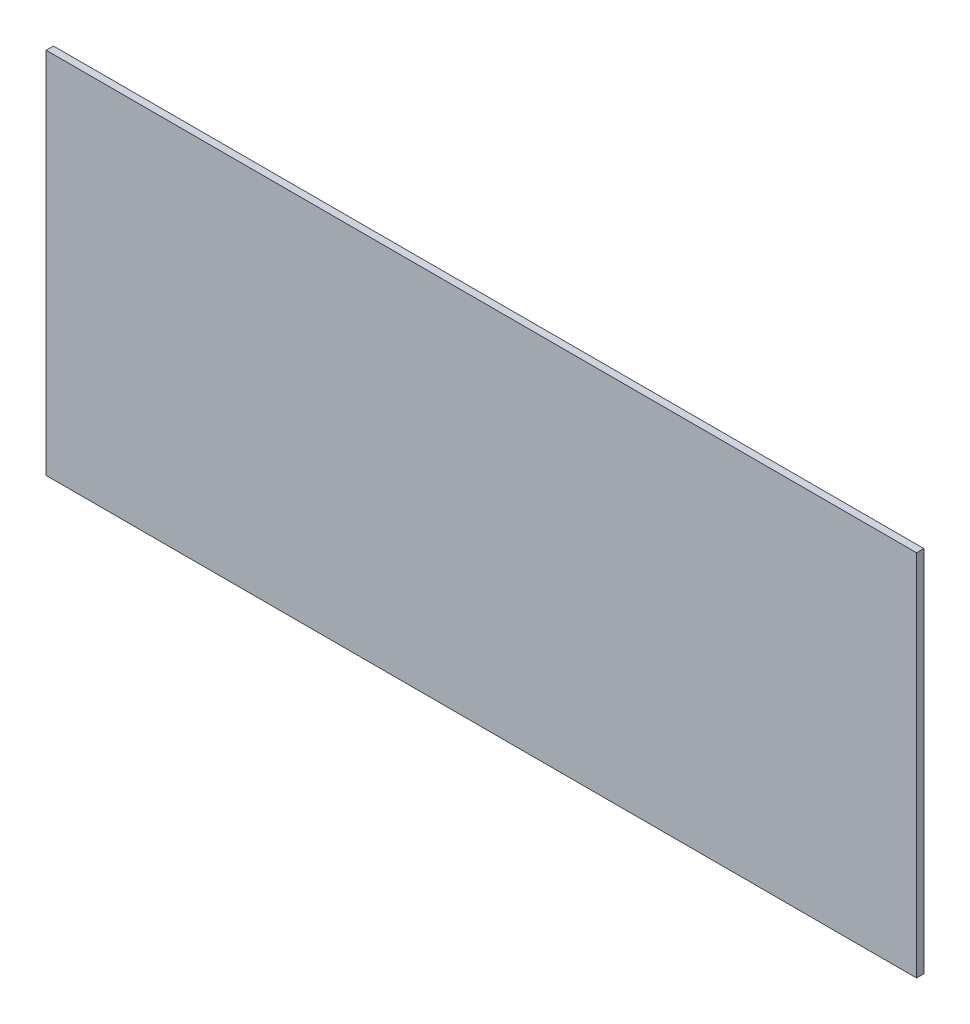
SolidWorks part; units mm, degrees
material "Acrylic (Medium-high impact)"
ref_plane "Front Plane" through (0, 0, 0) normal (0, 0, 1) x (1, 0, 0)
ref_plane "Top Plane" through (0, 0, 0) normal (0, 1, 0) x (1, 0, 0)
ref_plane "Right Plane" through (0, 0, 0) normal (1, 0, 0) x (0, 0, -1)
sketch "Sketch1" plane through (0, 0, 0) normal (0, 0, 1) x (1, 0, 0)
  line L1 (-268.25, -113.5) -> (268.25, -113.5)
  line L2 (-268.25, -113.5) -> (-268.25, 113.5)
  line L3 (-268.25, 113.5) -> (268.25, 113.5)
  line L4 (268.25, -113.5) -> (268.25, 113.5)
  line L5 (-268.25, -113.5) -> (268.25, 113.5) construction
  line L6 (-268.25, 113.5) -> (268.25, -113.5) construction
  point P0 (0, 0)
  dimension "D1" = 536.5
  dimension "D2" = 227
extrude "Boss-Extrude1" add sketch "Sketch1" along normal mid plane 4.4958
